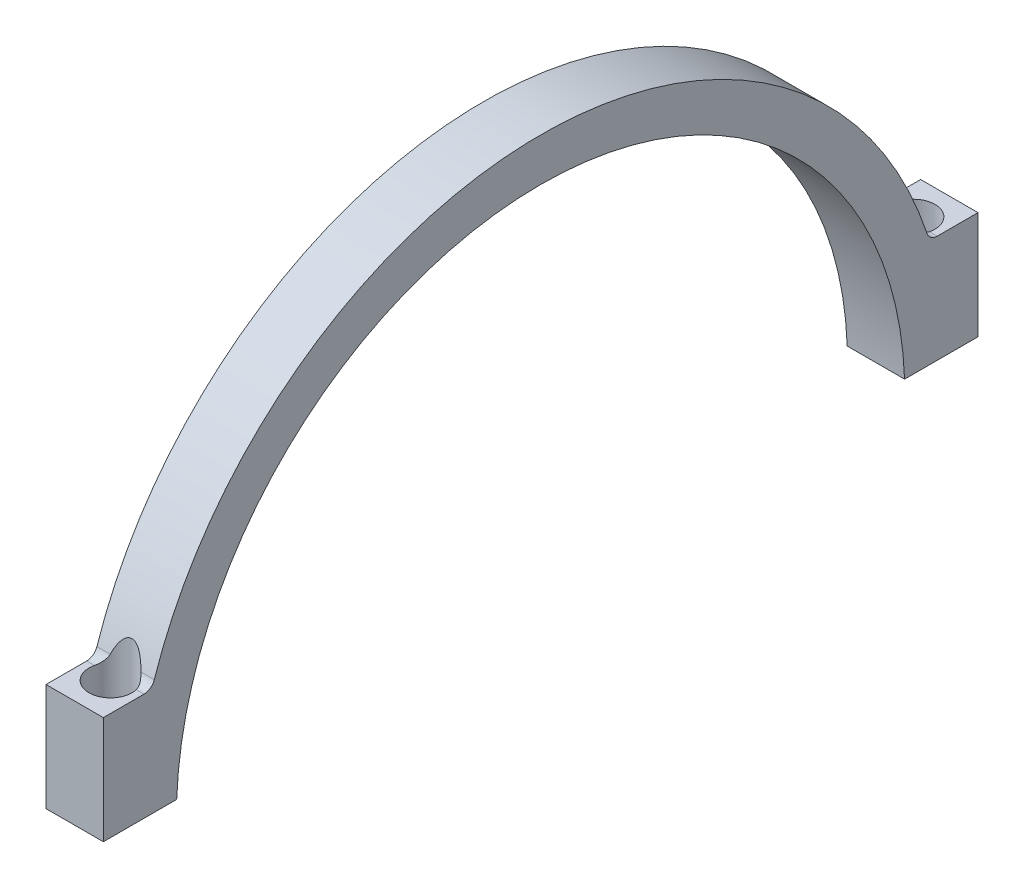
SolidWorks part; units mm, degrees
material "1060 Alloy"
ref_plane "Front Plane" through (0, 0, 0) normal (0, 0, 1) x (1, 0, 0)
ref_plane "Top Plane" through (0, 0, 0) normal (0, 1, 0) x (1, 0, 0)
ref_plane "Right Plane" through (0, 0, 0) normal (1, 0, 0) x (0, 0, -1)
sketch "Sketch1" plane through (0, 0, 0) normal (1, 0, 0) x (0, 0, -1)
  line L2 (-60.9955, 1.9) -> (-50.7645, 1.9)
  line L3 (50.7645, 1.9) -> (61.0045, 1.9)
  line L4 (-60.9955, 1.9) -> (-60.9955, 16.9)
  line L5 (-60.9955, 16.9) -> (-55.3202, 16.9)
  line L6 (61.0045, 1.9) -> (61.0045, 16.9)
  line L7 (61.0045, 16.9) -> (55.3202, 16.9)
  arc A0 (50.7645, 1.9) -> (-50.7645, 1.9) centre (0, 0) ccw
  arc A1 (53.8969, 17.9266) -> (-53.8969, 17.9266) centre (0, 0) ccw
  circle A2 centre (0, 0) radius 56.8 construction
  circle A3 centre (0, 0) radius 50.8 construction
  arc A5 (55.3202, 16.9) -> (53.8969, 17.9266) centre (55.3202, 18.4) cw
  arc A7 (-55.3202, 16.9) -> (-53.8969, 17.9266) centre (-55.3202, 18.4) ccw
  dimension "D1" = 101.6
  dimension "D2" = 122
  dimension "D3" = 15
  dimension "D6" = 10.24
  dimension "D4" = 15
  dimension "D7" = 1.9
  dimension "D8" = 1.9
  dimension "D5" = 6
extrude "Boss-Extrude1" add sketch "Sketch1" along normal blind 8
hole_wizard "M4 Clearance Hole1" positions "Sketch5" profile "Sketch4" hole size "M4" standard "ISO"
sketch "Sketch5" plane through (0, 16.9, 0) normal (0, 1, 0) x (1, 0, 0)
  line L0 (8, 61.0045) -> (8, 55.3202) construction
  line L1 (8, -60.9955) -> (0, -60.9955) construction
  line L2 (8, 61.0045) -> (0, 61.0045) construction
  line L4 (8, -55.3202) -> (8, -60.9955) construction
  point P0 (4, 56.0045)
  point P11 (4, -55.9955)
  dimension "D1" = 4
  dimension "D2" = 5
  dimension "D3" = 5
  dimension "D4" = 4
sketch "Sketch4" plane through (4, 16.9, -56.0045) normal (1, 0, 0) x (0, 0, 1)
  line L0 (0, 0) -> (0, 17.2919)
  line L1 (0, 17.2919) -> (2.15, 16)
  line L2 (2.15, 16) -> (2.15, 0)
  line L5 (2.15, 0) -> (0, 0)
  line L10 (0, 17.2919) -> (-2.15, 16) construction
  line L11 (0, -6.35) -> (0, 107.95) construction
  dimension "Hole Dia." = 4.3
  dimension "Hole Depth" = 16
  dimension "Drill Angle" = 118
sketch "Sketch7" plane through (0, 16.9, 0) normal (0, 1, 0) x (1, 0, 0)
  circle A0 centre (4, 56.0045) radius 3
  circle A1 centre (4, -55.9955) radius 3
  dimension "D1" = 6
  dimension "D2" = 6
extrude "Cut-Extrude1" cut sketch "Sketch7" against normal blind 6 and the other way blind 10
